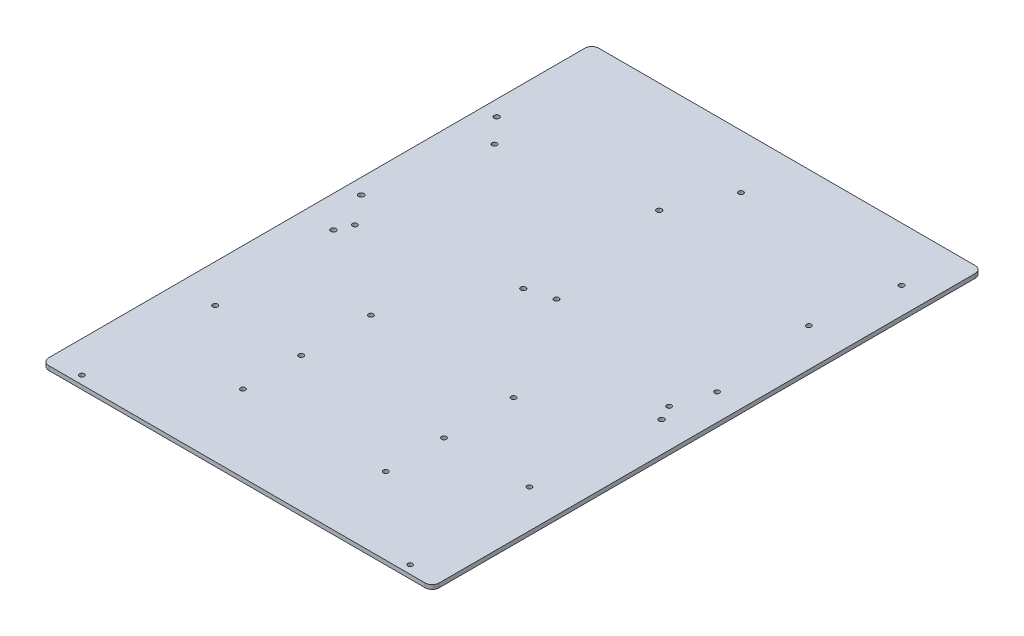
SolidWorks part; units mm, degrees
ref_plane "Front Plane" through (0, 0, 0) normal (0, 0, 1) x (1, 0, 0)
ref_plane "Top Plane" through (0, 0, 0) normal (0, 1, 0) x (1, 0, 0)
ref_plane "Right Plane" through (0, 0, 0) normal (1, 0, 0) x (0, 0, -1)
sketch "Sketch1" plane through (0, 0, 0) normal (0, 1, 0) x (1, 0, 0)
  line L1 (-139.7, 196.85) -> (139.7, 196.85)
  line L2 (-139.7, 196.85) -> (-139.7, -196.85)
  line L3 (-139.7, -196.85) -> (139.7, -196.85)
  line L4 (139.7, 196.85) -> (139.7, -196.85)
  line L5 (-139.7, 196.85) -> (139.7, -196.85) construction
  line L6 (-139.7, -196.85) -> (139.7, 196.85) construction
  point P0 (0, 0)
  dimension "D1" = 279.4
  dimension "D2" = 393.7
extrude "Boss-Extrude1" add sketch "Sketch1" along normal blind 3
sketch "Sketch2" plane through (0, 3, 0) normal (0, 1, 0) x (1, 0, 0)
  circle A0 centre (-117.0203, -190.8873) radius 1.716
  circle A1 centre (5.71, 158.1442) radius 1.75
  circle A2 centre (120.71, 158.1442) radius 1.75
  circle A3 centre (120.71, 26.1442) radius 1.75
  circle A4 centre (5.71, 26.1442) radius 1.75
  circle A5 centre (117.9797, -190.8873) radius 1.7
  circle A6 centre (-117.0203, -10.8873) radius 1.8709
  circle A7 centre (117.9797, -10.8873) radius 1.8833
  circle A8 centre (-128.7083, 117.7869) radius 1.837
  circle A9 centre (-128.7083, 20.7869) radius 1.9242
  circle A10 centre (-12.7083, 20.7869) radius 1.847
  circle A11 centre (-12.5746, 117.9206) radius 1.8616
extrude "Cut-Extrude1" cut sketch "Sketch2" against normal through all
sketch "Sketch3" plane through (0, 3, 0) normal (0, 1, 0) x (1, 0, 0)
  circle A0 centre (-112.5, -100) radius 1.75
  circle A1 centre (112.5, -100) radius 1.75
  circle A2 centre (-112.5, 100) radius 1.75
  circle A3 centre (112.5, 100) radius 1.75
  circle A4 centre (-112.5, 0) radius 1.75
  circle A5 centre (112.5, 0) radius 1.75
  point P12 (0, 0)
  dimension "D1" = 100
  dimension "D2" = 100
  dimension "D3" = 225
  dimension "D5" = 3.5
  dimension "D4" = 112.5
extrude "Cut-Extrude2" cut sketch "Sketch3" against normal through all
sketch "Sketch4" plane through (0, 3, 0) normal (0, 1, 0) x (1, 0, 0)
  circle A0 centre (-50.7594, -100.1938) radius 1.75
  circle A1 centre (51.456, -100.1938) radius 1.75
  circle A2 centre (-50.7594, -50.2972) radius 1.75
  circle A3 centre (51.456, -50.2972) radius 1.75
  circle A4 centre (-50.7594, -141.8551) radius 1.75
  circle A5 centre (51.456, -141.8551) radius 1.75
  dimension "D1" = 3.5
extrude "Cut-Extrude3" cut sketch "Sketch4" against normal through all
fillet "Fillet1" radius 5 4 edges at (-139.7, 1.5, -196.85) (139.7, 1.5, -196.85) (-139.7, 1.5, 196.85) (139.7, 1.5, 196.85)
